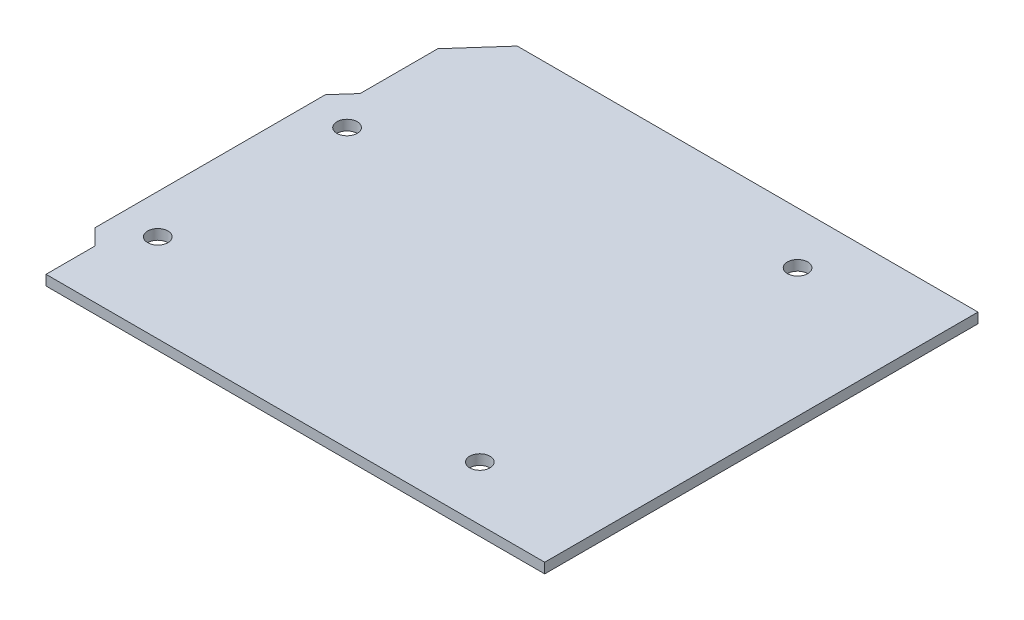
SolidWorks part; units mm, degrees
ref_plane "Front Plane" through (0, 0, 0) normal (0, 0, 1) x (1, 0, 0)
ref_plane "Top Plane" through (0, 0, 0) normal (0, 1, 0) x (1, 0, 0)
ref_plane "Right Plane" through (0, 0, 0) normal (1, 0, 0) x (0, 0, -1)
sketch "Sketch5" plane through (0, 0, 0) normal (0, 1, 0) x (1, 0, 0)
  line L0 (-31.9362, 32.1641) -> (-37.4686, 25.9516)
  line L1 (-31.9362, 32.1641) -> (36.1142, 32.1641)
  line L2 (-31.6124, -31.8359) -> (36.1142, -31.8359)
  line L3 (36.1142, 32.1641) -> (36.1142, -31.8359)
  line L4 (-37.4686, 25.9516) -> (-37.4686, 14.4831)
  line L5 (-37.4686, 14.4831) -> (-39.8858, 11.7688)
  line L6 (-39.8858, 11.7688) -> (-39.8858, -22.2645)
  line L7 (-39.8858, -22.2645) -> (-37.548, -24.6023)
  line L8 (-37.548, -24.6023) -> (-37.548, -31.8359)
  line L9 (-37.548, -31.8359) -> (-31.6124, -31.8359)
  dimension "D1" = 64
extrude "Boss-Extrude3" add sketch "Sketch5" along normal blind 1.5
sketch "Sketch3" plane through (0, 0, 0) normal (0, 1, 0) x (1, 0, 0)
  circle A0 centre (-34.0859, 9.1715) radius 1.5
  circle A1 centre (-34.085, -18.7847) radius 1.5
  circle A2 centre (17.1262, 24.5034) radius 1.5
  circle A3 centre (18.505, -23.8098) radius 1.5
  dimension "D1" = 3
  dimension "D2" = 3
  dimension "D3" = 3
  dimension "D4" = 3
extrude "Cut-Extrude6" cut sketch "Sketch3" along normal blind 1.5
